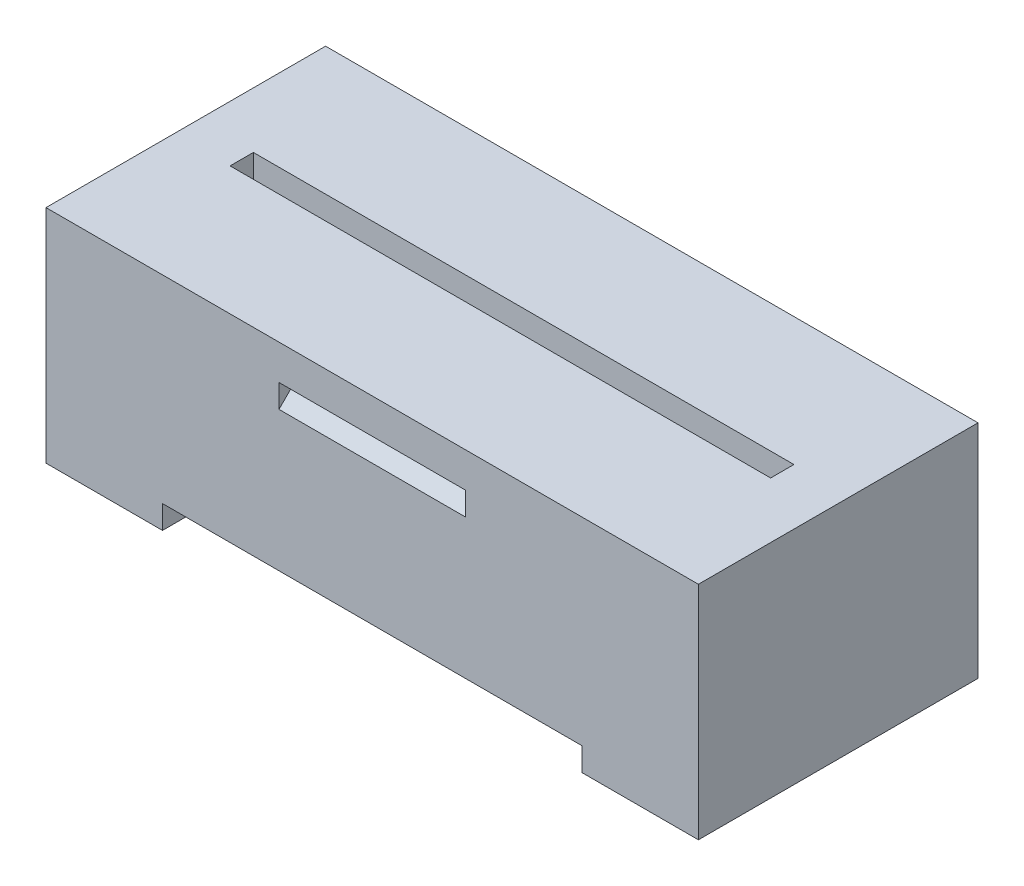
SolidWorks part; units mm, degrees
ref_plane "Přední rovina" through (0, 0, 0) normal (0, 0, 1) x (1, 0, 0)
ref_plane "Horní rovina" through (0, 0, 0) normal (0, 1, 0) x (1, 0, 0)
ref_plane "Pravá rovina" through (0, 0, 0) normal (1, 0, 0) x (0, 0, -1)
sketch "Skica1" plane through (0, 0, 0) normal (0, 0, 1) x (1, 0, 0)
  line L5 (-18.6567, 1.7853) -> (-46.6567, 1.7853)
  line L10 (-18.6567, 1.7853) -> (-18.6567, -6.7147)
  line L11 (-46.6567, 1.7853) -> (-46.6567, -6.7147)
  line L12 (-46.6567, -6.7147) -> (-18.6567, -6.7147)
  dimension "D1" = 8.5
  dimension "D6" = 28
extrude "Přidat vysunutím1" add sketch "Skica1" along normal blind 12 contours L5 L11 L12 L10
sketch "Skica3" plane through (0, -6.7147, 0) normal (0, -1, 0) x (-1, 0, 0)
  line L4 (46.6567, -12) -> (46.6567, 0) construction
  line L5 (46.6567, 0) -> (18.6567, 0) construction
  line L6 (18.6567, -12) -> (18.6567, 0) construction
  circle A4 centre (41.6567, -6) radius 2.6
  circle A5 centre (35.6467, -6) radius 2.6
  circle A6 centre (29.6367, -6) radius 2.6
  circle A7 centre (23.6267, -6) radius 2.6
  dimension "D1" = 5.2
  dimension "D4" = 4
  dimension "D3" = 6
  dimension "D5" = 4.97
  dimension "D2" = 5
extrude "Odebrat vysunutím2" cut sketch "Skica3" against normal blind 7.5
sketch "Skica4" plane through (0, 1.7853, 0) normal (0, 1, 0) x (1, 0, 0)
  line L1 (-44.2567, -5.5) -> (-21.0567, -5.5)
  line L2 (-44.2567, -5.5) -> (-44.2567, -6.5)
  line L3 (-44.2567, -6.5) -> (-21.0567, -6.5)
  line L4 (-21.0567, -5.5) -> (-21.0567, -6.5)
  line L5 (-44.2567, -5.5) -> (-21.0567, -6.5) construction
  line L6 (-44.2567, -6.5) -> (-21.0567, -5.5) construction
  line L7 (-18.6567, -12) -> (-18.6567, 0) construction
  line L8 (-18.6567, -12) -> (-46.6567, -12) construction
  line L9 (-46.6567, -12) -> (-46.6567, 0) construction
  point P0 (-32.6567, -6)
  dimension "D1" = 1
  dimension "D2" = 23.2
  dimension "D3" = 5.5
  dimension "D4" = 2.4
  dimension "D5" = 2.4
extrude "Odebrat vysunutím3" cut sketch "Skica4" against normal blind 1
sketch "Skica5" plane through (0, -6.7147, 0) normal (0, -1, 0) x (-1, 0, 0)
  line L1 (46.6567, -12) -> (41.6567, -12)
  line L2 (46.6567, -12) -> (46.6567, 0)
  line L3 (46.6567, 0) -> (41.6567, 0)
  line L4 (41.6567, -12) -> (41.6567, 0)
  line L5 (18.6567, -12) -> (23.6567, -12)
  line L6 (18.6567, -12) -> (18.6567, 0)
  line L7 (18.6567, 0) -> (23.6567, 0)
  line L8 (23.6567, -12) -> (23.6567, 0)
  dimension "D1" = 12
  dimension "D2" = 5
  dimension "D3" = 12
  dimension "D4" = 5
extrude "Přidat vysunutím2" add sketch "Skica5" along normal blind 1
sketch "Skica6" plane through (0, -7.7147, 0) normal (0, -1, 0) x (-1, 0, 0)
  line L0 (41.6567, -12) -> (46.6567, -12) construction
  line L1 (45.6567, -11) -> (41.6567, -11)
  line L2 (45.6567, -11) -> (45.6567, -1)
  line L3 (45.6567, -1) -> (41.6567, -1)
  line L4 (41.6567, -11) -> (41.6567, -1)
  line L5 (46.6567, -12) -> (46.6567, 0) construction
  line L6 (18.6567, -12) -> (23.6567, -12) construction
  line L7 (19.6567, -11) -> (23.6567, -11)
  line L8 (19.6567, -11) -> (19.6567, -1)
  line L9 (19.6567, -1) -> (23.6567, -1)
  line L10 (23.6567, -11) -> (23.6567, -1)
  line L11 (18.6567, 0) -> (18.6567, -12) construction
  dimension "D1" = 10
  dimension "D2" = 4
  dimension "D3" = 1
  dimension "D4" = 1
  dimension "D5" = 10
  dimension "D6" = 4
  dimension "D7" = 1
  dimension "D8" = 1
extrude "Odebrat vysunutím4" cut sketch "Skica6" against normal blind 1
sketch "Skica9" plane through (-18.6567, 0, 0) normal (1, 0, 0) x (0, 0, -1)
  line L0 (-12, 0.2853) -> (-11, 0.2853)
  line L1 (-12, 1.7853) -> (-12, -7.7147) construction
  line L2 (-11, 0.2853) -> (-12, -0.7147)
  line L3 (-12, -0.7147) -> (-12, 0.2853)
  line L4 (0, 0.2853) -> (-1, 0.2853)
  line L5 (0, 1.7853) -> (0, -7.7147) construction
  line L6 (-1, 0.2853) -> (0, -0.7147)
  line L7 (0, -0.7147) -> (0, 0.2853)
  dimension "D1" = 1
  dimension "D2" = 8
  dimension "D3" = 1
  dimension "D4" = 1
extrude "Odebrat vysunutím5" cut sketch "Skica9" against normal blind 8 from offset 10
